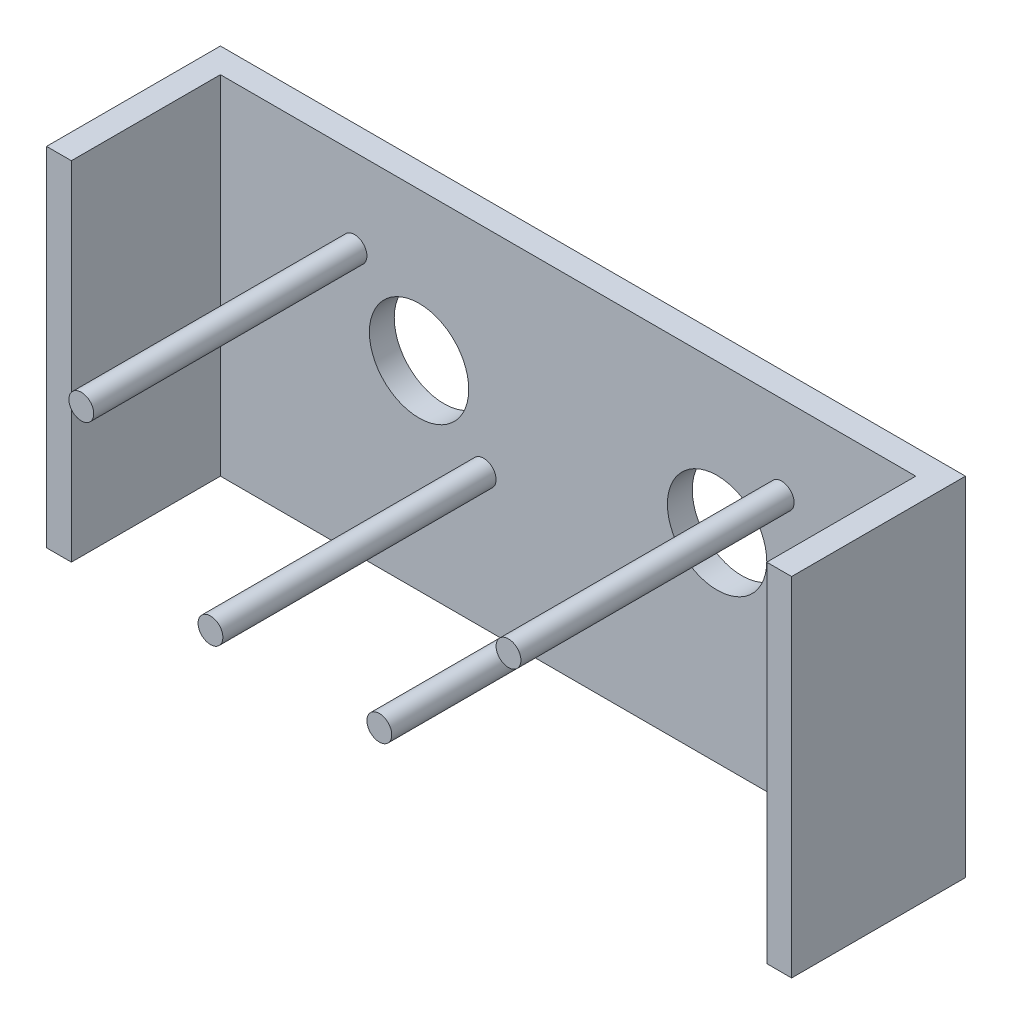
SolidWorks part; units mm, degrees
ref_plane "Plan de face" through (0, 0, 0) normal (0, 0, 1) x (1, 0, 0)
ref_plane "Plan de dessus" through (0, 0, 0) normal (0, 1, 0) x (1, 0, 0)
ref_plane "Plan de droite" through (0, 0, 0) normal (1, 0, 0) x (0, 0, -1)
sketch "Esquisse1" plane through (0, 0, 0) normal (0, 0, 1) x (1, 0, 0)
  line L1 (-66.9192, 34.5173) -> (83.0808, 34.5173)
  line L2 (-66.9192, 34.5173) -> (-66.9192, -35.4827)
  line L3 (-66.9192, -35.4827) -> (83.0808, -35.4827)
  line L4 (83.0808, 34.5173) -> (83.0808, -35.4827)
  dimension "D1" = 70
  dimension "D2" = 150
extrude "Boss.-Extru.1" add sketch "Esquisse1" along normal blind 5
sketch "Esquisse2" plane through (0, 0, 5) normal (0, 0, 1) x (1, 0, 0)
  line L0 (-66.9192, -35.4827) -> (83.0808, -35.4827) construction
  line L1 (-66.9192, 34.5173) -> (-61.9192, 34.5173)
  line L2 (-66.9192, 34.5173) -> (-66.9192, -35.4827)
  line L3 (-66.9192, -35.4827) -> (-61.9192, -35.4827)
  line L4 (-61.9192, 34.5173) -> (-61.9192, -35.4827)
  line L6 (83.0808, 34.5173) -> (78.0808, 34.5173)
  line L7 (83.0808, 34.5173) -> (83.0808, -35.4827)
  line L8 (83.0808, -35.4827) -> (78.0808, -35.4827)
  line L9 (78.0808, 34.5173) -> (78.0808, -35.4827)
  dimension "D1" = 5
  dimension "D2" = 5
extrude "Boss.-Extru.2" add sketch "Esquisse2" along normal blind 30
sketch "Esquisse3" plane through (0, 0, 0) normal (0, 0, -1) x (-1, 0, 0)
  line L0 (66.9192, 34.5173) -> (66.9192, -35.4827) construction
  line L2 (66.9192, -35.4827) -> (-83.0808, -35.4827) construction
  line L3 (21.9192, 4.6473) -> (-83.0808, 4.6473) construction
  line L4 (-83.0808, -35.4827) -> (-83.0808, 34.5173) construction
  circle A0 centre (21.9192, 4.6473) radius 10
  circle A1 centre (-38.0808, 4.6473) radius 10
  dimension "D3" = 20
  dimension "D4" = 20
  dimension "D1" = 45
  dimension "D2" = 40.13
  dimension "D5" = 60
extrude "Enlèv. mat.-Extru.1" cut sketch "Esquisse3" against normal blind 30
sketch "Esquisse5" plane through (0, 0, 0) normal (0, 0, -1) x (-1, 0, 0)
  line L0 (-38.0808, 4.6473) -> (-67.1678, 4.6473) construction
  line L1 (-58.0808, 24.6473) -> (-18.0808, 24.6473)
  line L2 (-58.0808, 24.6473) -> (-58.0808, -15.3527)
  line L3 (-58.0808, -15.3527) -> (-18.0808, -15.3527)
  line L4 (-18.0808, 24.6473) -> (-18.0808, -15.3527)
  line L5 (1.9192, 24.6473) -> (41.9192, 24.6473)
  line L6 (1.9192, 24.6473) -> (1.9192, -15.3527)
  line L7 (1.9192, -15.3527) -> (41.9192, -15.3527)
  line L8 (41.9192, 24.6473) -> (41.9192, -15.3527)
  line L9 (-67.1678, 4.6473) -> (-24.0706, 4.6473) construction
  line L10 (-24.0706, 4.6473) -> (42.106, 4.6473) construction
  line L11 (-38.0808, 30.3585) -> (-38.0808, -24.5139) construction
  line L12 (21.9192, 4.6473) -> (21.9192, -26.6335) construction
  circle A0 centre (-51.0808, 17.6473) radius 2.5
  circle A1 centre (-25.0808, -8.3527) radius 2.5
  circle A2 centre (8.9192, -8.3527) radius 2.5
  circle A3 centre (34.9192, 17.6473) radius 2.5
  dimension "D9" = 5
  dimension "D10" = 5
  dimension "D11" = 5
  dimension "D12" = 5
  dimension "D1" = 40
  dimension "D2" = 40
  dimension "D3" = 40
  dimension "D4" = 40
  dimension "D5" = 20
  dimension "D6" = 20
  dimension "D7" = 20
  dimension "D8" = 20
  dimension "D13" = 7
  dimension "D14" = 7
  dimension "D15" = 7
  dimension "D16" = 7
  dimension "D17" = 7
  dimension "D18" = 7
  dimension "D19" = 7
  dimension "D20" = 7
extrude "Boss.-Extru.3" add sketch "Esquisse5" against normal blind 60 contours A3 | A2 | A0 | A1
